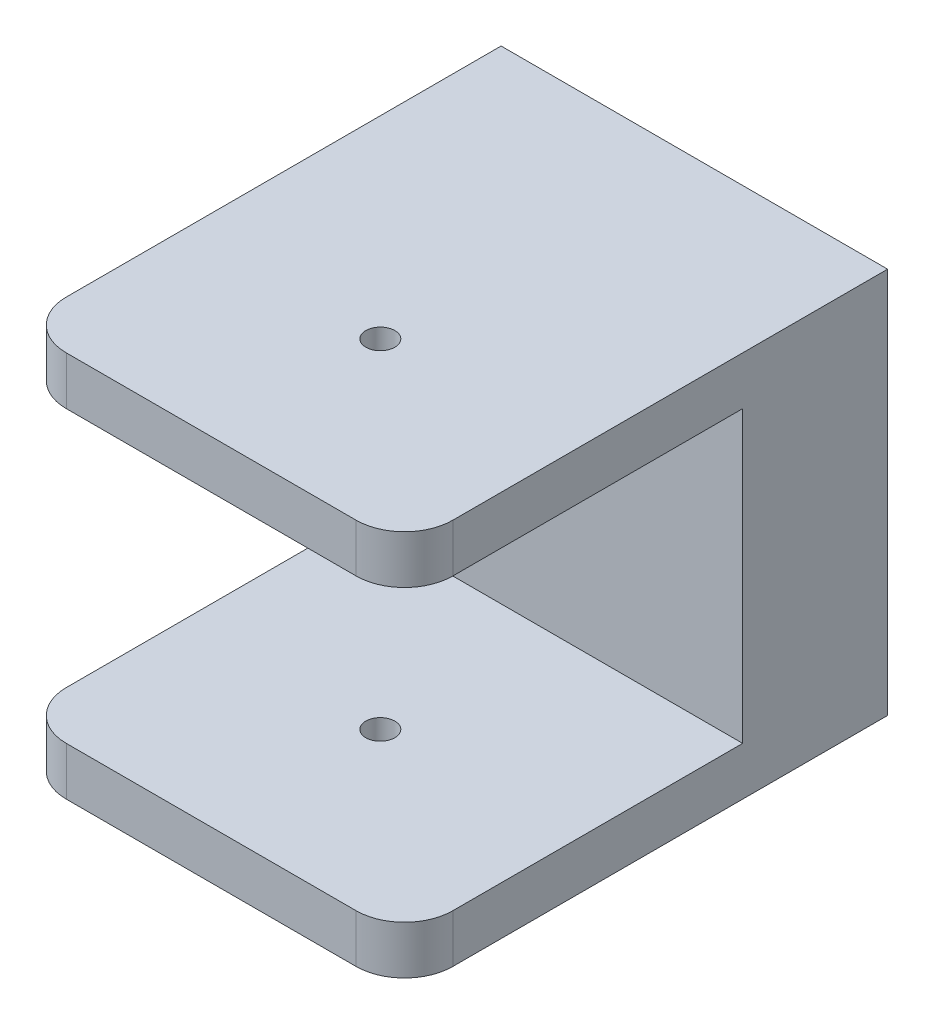
SolidWorks part; units mm, degrees
material "ABS"
ref_plane "Front Plane" through (0, 0, 0) normal (0, 0, 1) x (1, 0, 0)
ref_plane "Top Plane" through (0, 0, 0) normal (0, 1, 0) x (1, 0, 0)
ref_plane "Right Plane" through (0, 0, 0) normal (1, 0, 0) x (0, 0, -1)
sketch "Sketch1" plane through (0, 0, 0) normal (0, 0, 1) x (1, 0, 0)
  line L0 (40, 80) -> (40, 0) construction
  line L1 (0, 0) -> (80, 0)
  line L2 (0, 0) -> (0, 80)
  line L3 (0, 80) -> (80, 80)
  line L4 (80, 0) -> (80, 80)
  line L5 (0, 40) -> (80, 40) construction
  circle A0 centre (40, 40) radius 3
  dimension "D3" = 6
  dimension "D1" = 80
  dimension "D2" = 80
extrude "Boss-Extrude1" add sketch "Sketch1" along normal blind 100
sketch "Sketch2" plane through (0, 0, 100) normal (0, 0, 1) x (1, 0, 0)
  line L6 (80, 40) -> (0, 40) construction
  line L7 (0, 80) -> (0, 0) construction
  line L8 (0, 10) -> (0, 70)
  line L9 (80, 10) -> (80, 70)
  line L10 (80, 0) -> (80, 80) construction
  line L11 (0, 10) -> (80, 10)
  line L12 (80, 70) -> (0, 70)
  point P7 (0, 40)
  point P12 (80, 40)
  dimension "D1" = 60
  dimension "D2" = 60
extrude "Cut-Extrude1" cut sketch "Sketch2" against normal blind 70
sketch "Sketch3" plane through (0, 80, 0) normal (0, 1, 0) x (1, 0, 0)
  line L0 (80, -30) -> (0, -30) construction
  line L1 (80, -30) -> (0, -30) construction
  line L2 (40, -30) -> (40, -100) construction
  line L3 (80, -100) -> (0, -100) construction
  line L4 (40, -65) -> (0, -65) construction
  line L5 (0, -100) -> (0, 0) construction
  circle A1 centre (40, -65) radius 3
  dimension "D1" = 6
extrude "Cut-Extrude2" cut sketch "Sketch3" against normal through all both and the other way through all
fillet "Fillet1" radius 10 4 edges at (80, 5, 100) (0, 5, 100) (80, 75, 100) (0, 75, 100)
